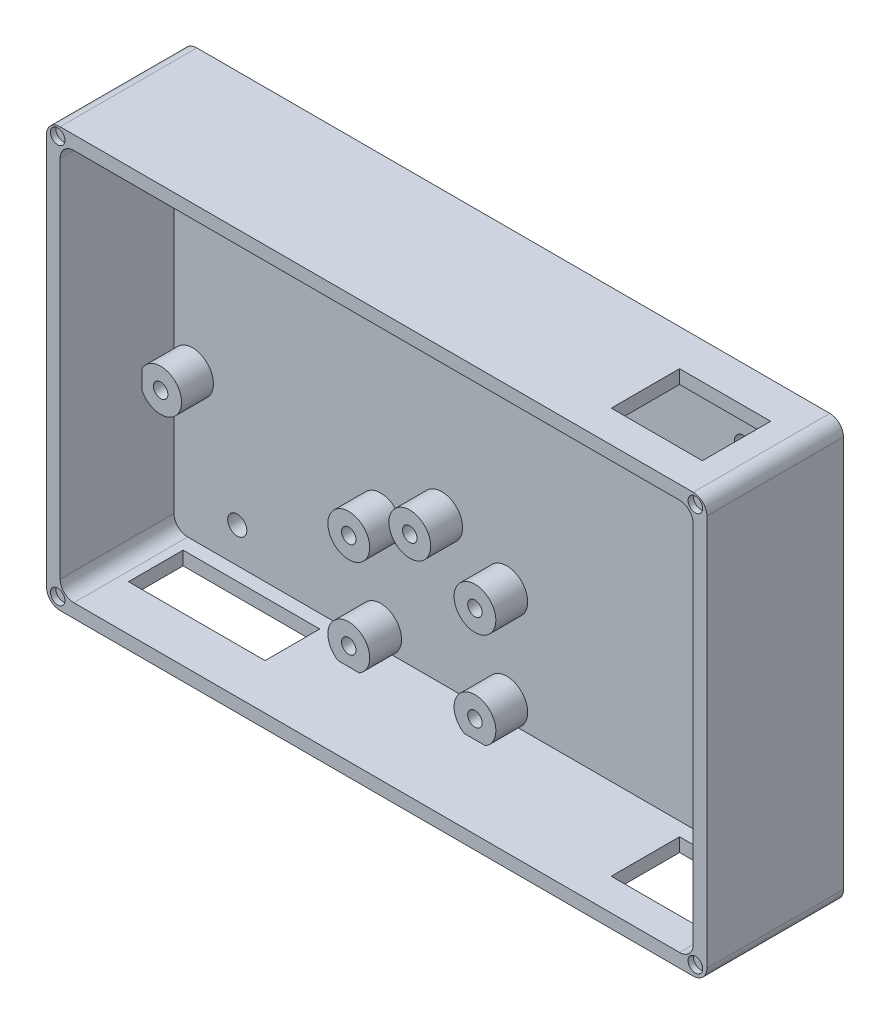
SolidWorks part; units mm, degrees
ref_plane "Alzado" through (0, 0, 0) normal (0, 0, 1) x (1, 0, 0)
ref_plane "Planta" through (0, 0, 0) normal (0, 1, 0) x (1, 0, 0)
ref_plane "Vista lateral" through (0, 0, 0) normal (1, 0, 0) x (0, 0, -1)
sketch "Croquis1" plane through (0, 0, 0) normal (0, 0, 1) x (1, 0, 0)
  line L1 (3, 0) -> (142, 0)
  line L2 (0, -3) -> (0, -89)
  line L3 (3, -92) -> (142, -92)
  line L4 (145, -3) -> (145, -89)
  arc A0 (0, -89) -> (3, -92) centre (3, -89) ccw
  arc A1 (142, -92) -> (145, -89) centre (142, -89) ccw
  arc A2 (142, 0) -> (145, -3) centre (142, -3) cw
  arc A3 (3, 0) -> (0, -3) centre (3, -3) ccw
  point P7 (0, -92)
  point P12 (145, 0)
  point P15 (0, 0)
  dimension "D3" = 3
  dimension "D1" = 92
  dimension "D2" = 145
extrude "Forma" add sketch "Croquis1" along normal blind 5
sketch "Croquis4" plane through (0, 0, 5) normal (0, 0, 1) x (1, 0, 0)
  line L0 (94.0252, -92) -> (123.2656, -92) construction
  line L1 (3, -92) -> (142, -92) construction
  line L2 (145, -58.6654) -> (145, -77.0971) construction
  line L3 (145, -89) -> (145, -3) construction
  line L9 (3, 0) -> (142, 0)
  line L10 (0, -3) -> (0, -89)
  line L11 (3, -92) -> (142, -92)
  line L12 (145, -3) -> (145, -89)
  line L16 (3, -89) -> (142, -89)
  line L17 (142, -89) -> (142, -3)
  line L18 (142, -3) -> (3, -3)
  line L19 (3, -3) -> (3, -89)
  line L20 (6, -89) -> (139, -89)
  line L21 (142, -86) -> (142, -6)
  line L22 (139, -3) -> (6, -3)
  line L23 (3, -6) -> (3, -86)
  arc A4 (0, -89) -> (3, -92) centre (3, -89) ccw
  arc A5 (142, -92) -> (145, -89) centre (142, -89) ccw
  arc A6 (142, 0) -> (145, -3) centre (142, -3) cw
  arc A7 (3, 0) -> (0, -3) centre (3, -3) ccw
  arc A8 (142, -6) -> (139, -3) centre (139, -6) ccw
  arc A9 (139, -89) -> (142, -86) centre (139, -86) ccw
  arc A10 (6, -89) -> (3, -86) centre (6, -86) cw
  arc A11 (6, -3) -> (3, -6) centre (6, -6) ccw
  point P31 (145, -92)
  point P37 (0, 0)
  dimension "D2" = 3
  dimension "D3" = 3
  dimension "D1" = 3
extrude "Marco" add sketch "Croquis4" along normal blind 25 contours A7 L9 A6 L12 A5 L11 A4 L10 | A10 L20 A9 L21 A8 L22 A11 L23
sketch "Croquis5" plane through (0, 0, 5) normal (0, 0, 1) x (1, 0, 0)
  line L0 (0, 0) -> (7.0711, -7.0711) construction
  line L1 (7.0711, -7.0711) -> (7.0711, -57.0711) construction
  line L2 (0, -3) -> (0, -89) construction
  line L3 (7.0711, -7.0711) -> (61.7711, -7.0711) construction
  line L4 (61.7711, -8.6586) -> (61.7711, -55.4836) construction
  line L5 (8.6586, -7.0711) -> (60.1836, -7.0711)
  line L6 (61.7711, -57.0711) -> (7.0711, -57.0711) construction
  circle A0 centre (7.0711, -7.0711) radius 1.5875
  circle A1 centre (7.0711, -57.0711) radius 1.5875
  circle A2 centre (61.7711, -7.0711) radius 1.5875
  circle A3 centre (61.7711, -57.0711) radius 1.5875
  circle A4 centre (7.0711, -7.0711) radius 4.5875
  circle A5 centre (61.7711, -7.0711) radius 4.5875
  circle A6 centre (7.0711, -57.0711) radius 4.5875
  circle A7 centre (61.7711, -57.0711) radius 4.5875
  dimension "D3" = 3.175
  dimension "D4" = 3.175
  dimension "D6" = 3.175
  dimension "D8" = 3.175
  dimension "D1" = 45
  dimension "D2" = 10
  dimension "D5" = 50
  dimension "D7" = 54.7
  dimension "D10" = 51.525
  dimension "D11" = 46.825
  dimension "D9" = 3
extrude "BasePCB" add sketch "Croquis5" along normal blind 7
sketch "Croquis6" plane through (0, 0, 5) normal (0, 0, 1) x (1, 0, 0)
  line L0 (3, -73.0692) -> (43, -73.0692) construction
  line L1 (3, -59.1857) -> (3, -86) construction
  line L3 (48.3742, -64.0341) -> (75.8742, -64.0341)
  line L4 (48.3742, -64.0341) -> (48.3742, -85.0341)
  line L5 (48.3742, -85.0341) -> (75.8742, -85.0341)
  line L6 (75.8742, -64.0341) -> (75.8742, -85.0341)
  circle A0 centre (48.3742, -64.0341) radius 1.5875
  circle A1 centre (48.3742, -64.0341) radius 4.5875
  circle A2 centre (76.0742, -64.0341) radius 4.5875
  circle A3 centre (76.0742, -64.0341) radius 1.5875
  circle A4 centre (76.0742, -85.0341) radius 4.5875
  circle A5 centre (76.0742, -85.0341) radius 1.5875
  circle A6 centre (48.3742, -85.0341) radius 4.5875
  circle A7 centre (48.3742, -85.0341) radius 1.5875
  line M7 (6, -89) -> (139, -89)
  dimension "D2" = 3.175
  dimension "D1" = 40
  dimension "D3" = 27.5
  dimension "D4" = 21
  dimension "D5" = 3
  dimension "D6" = 2
  dimension "D7" = 2
extrude "SujeciónRelé" add sketch "Croquis6" along normal blind 7 contours L3 A1 L4 A0 | L4 A1 L3 A0 | A3 L6 A2 L3 | A3 L3 A2 L6 | A5 L5 A4 L6 M7 | A5 L6 A4 L5 | A7 L4 A6 L5 M7 | A7 L5 A6 L4
sketch "Croquis8" plane through (0, 0, 5) normal (0, 0, 1) x (1, 0, 0)
  line L0 (0, -81.8446) -> (0, -92) construction
  line L1 (0, -3) -> (0, -89) construction
  line L2 (127.2418, 0) -> (145, 0) construction
  line L3 (3, -92) -> (142, -92) construction
  line L4 (11.1592, -92) -> (0, -92) construction
  line L5 (3, 0) -> (142, 0) construction
  line L6 (0, -92) -> (145, 0) construction
  line L7 (145, -3) -> (145, -89) construction
  line L8 (145, -9.7054) -> (145, 0) construction
  line L9 (128.1124, -10.7149) -> (128.1124, -81.2851) construction
  line L10 (128.1124, -81.2851) -> (16.8876, -81.2851) construction
  circle A0 centre (16.8876, -81.2851) radius 2.1
  circle A1 centre (128.1124, -10.7149) radius 2.1
  circle A2 centre (128.1124, -81.2851) radius 2.1
  dimension "D2" = 4.2
  dimension "D3" = 4.2
  dimension "D5" = 4.2
  dimension "D1" = 20
  dimension "D4" = 20
extrude "BarrenosMuro" cut sketch "Croquis8" against normal blind 14
sketch "Croquis10" plane through (0, 0, 30) normal (0, 0, 1) x (1, 0, 0)
  line L0 (134.9723, -92) -> (149.9965, -92) construction
  line L1 (3, -92) -> (142, -92) construction
  line L2 (149.9965, -92) -> (145, -83.1815) construction
  line L3 (145, -3) -> (145, -89) construction
  line L4 (145, -83.1815) -> (145, -96.6275) construction
  line L5 (142.4631, -89.5887) -> (145, -92) construction
  circle A0 centre (142.4631, -89.5887) radius 1.6
  circle A1 centre (2.4631, -89.5887) radius 1.6
  circle A2 centre (2.4631, -2.0887) radius 1.6
  circle A3 centre (142.4631, -2.0887) radius 1.6
  dimension "D1" = 3.2
  dimension "D2" = 3.5
  dimension "D3" = 2
  dimension "D4" = 2
extrude "Cortar-Extruir2" cut sketch "Croquis10" against normal blind 1.2
sketch "Croquis11" plane through (0, -92, 0) normal (0, -1, 0) x (1, 0, 0)
  line L0 (3, 0) -> (142, 0) construction
  line L1 (8, 20) -> (38, 20)
  line L2 (8, 20) -> (8, 8)
  line L3 (8, 8) -> (38, 8)
  line L4 (38, 20) -> (38, 8)
  line L5 (0, 30) -> (0, 0) construction
  dimension "D1" = 30
  dimension "D2" = 12
  dimension "D3" = 8
  dimension "D4" = 8
extrude "Cortar-Extruir3" cut sketch "Croquis11" against normal blind 15
sketch "Croquis12" plane through (0, -92, 0) normal (0, -1, 0) x (1, 0, 0)
  line L1 (117, 23) -> (137, 23)
  line L2 (117, 23) -> (117, 8)
  line L3 (117, 8) -> (137, 8)
  line L4 (137, 23) -> (137, 8)
  line L5 (3, 0) -> (142, 0) construction
  line L6 (145, 30) -> (145, 0) construction
  dimension "D1" = 20
  dimension "D2" = 15
  dimension "D3" = 8
  dimension "D4" = 8
extrude "Cortar-Extruir4" cut sketch "Croquis12" against normal blind 101.1
